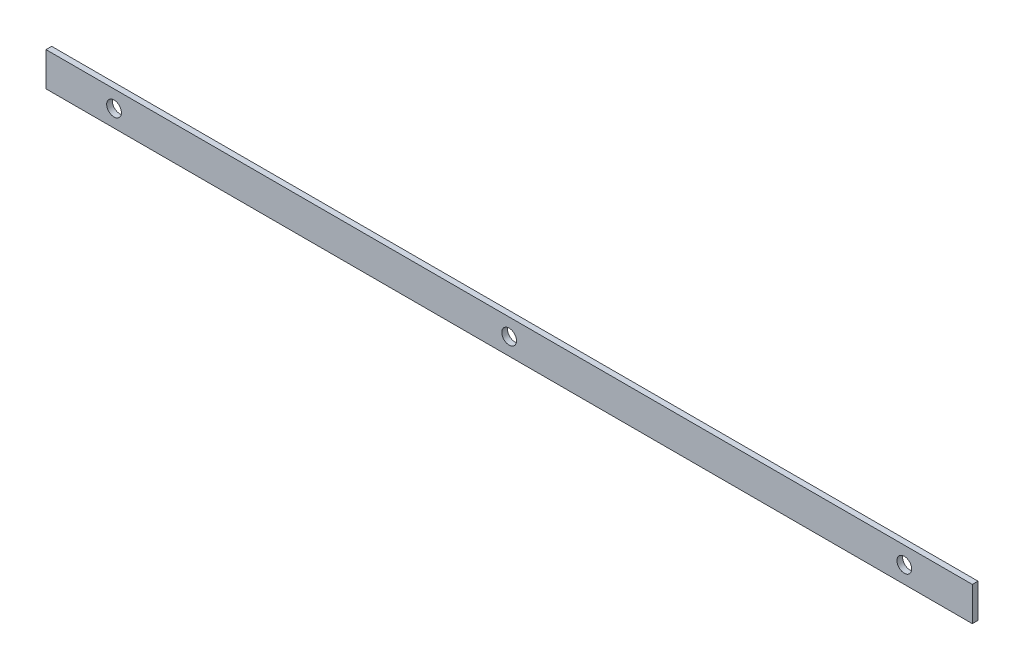
SolidWorks part; units mm, degrees
ref_plane "Plan de face" through (0, 0, 0) normal (0, 0, 1) x (1, 0, 0)
ref_plane "Plan de dessus" through (0, 0, 0) normal (0, 1, 0) x (1, 0, 0)
ref_plane "Plan de droite" through (0, 0, 0) normal (1, 0, 0) x (0, 0, -1)
sketch "Esquisse1" plane through (0, 0, 0) normal (0, 0, 1) x (1, 0, 0)
  line L0 (-408.5, 0) -> (408.5, 0)
other "Elément mécano-soudé1"
ref_plane "Plan1" through (-408.5, 0, 0) normal (1, 0, 0) x (0, 1, 0)
sketch "plat" plane through (-408.5, 0, 0) normal (1, 0, 0) x (0, 1, 0)
  line L0 (-15, 0) -> (15, 0) construction
  line L1 (-15, 2.5) -> (15, 2.5)
  line L2 (-15, 2.5) -> (-15, -2.5)
  line L3 (-15, -2.5) -> (15, -2.5)
  line L4 (15, 2.5) -> (15, -2.5)
  line L5 (0, 2.5) -> (0, -2.5) construction
  point P8 (0, 0)
  dimension "B" = 30
  dimension "A" = 5
sketch "Esquisse2" plane through (0, 0, -2.5) normal (0, 0, -1) x (-1, 0, 0)
  line L0 (408.5, 0) -> (-408.5, 0) construction
  line L1 (408.5, -15) -> (408.5, 15) construction
  line L2 (-408.5, -15) -> (-408.5, 15) construction
  point P0 (348.5, 0)
  point P5 (-348.5, 0)
ref_plane "Plan2" through (348.5, 0, 0) normal (1, 0, 0) x (0, 0, -1)
hole_wizard "Diamètre du perçage Ø13.0 (13)1" positions "Esquisse3" profile "Esquisse4" hole size "Ø13.0" standard "ISO" end condition through all
sketch "Esquisse3" plane through (0, 0, -2.5) normal (0, 0, -1) x (-1, 0, 0)
  point P0 (348.5, 0)
sketch "Esquisse4" plane through (-348.5, 0, -2.5) normal (1, 0, 0) x (0, 1, 0)
  line L0 (0, 0) -> (0, 5)
  line L1 (0, 5) -> (6.5, 5)
  line L2 (6.5, 5) -> (6.5, 0)
  line L5 (6.5, 0) -> (0, 0)
  line L11 (0, -6.35) -> (0, 107.95) construction
  dimension "Diamètre du perçage jusqu'au prochain" = 13
  dimension "Profondeur du perçage jusqu'au prochain" = 5
pattern_linear "Répétition linéaire2" count 3 spacing 348.5 along (1, 0, 0) of "Diamètre du perçage Ø13.0 (13)1"
equation "\"D2@Esquisse2\"=\"D1@Esquisse2\""
